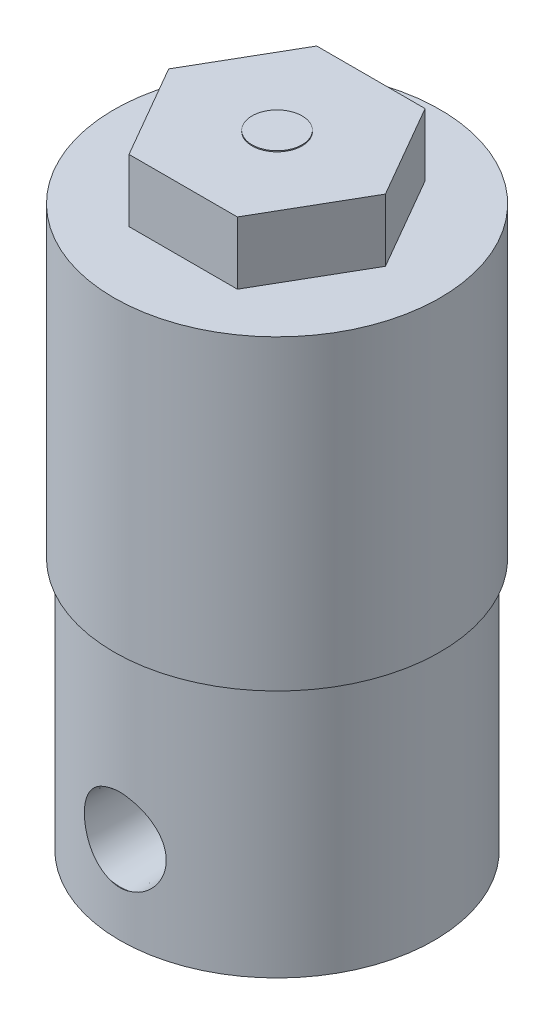
SolidWorks part; units mm, degrees
ref_plane "Plan de face" through (0, 0, 0) normal (0, 0, 1) x (1, 0, 0)
ref_plane "Plan de dessus" through (0, 0, 0) normal (0, 1, 0) x (1, 0, 0)
ref_plane "Plan de droite" through (0, 0, 0) normal (1, 0, 0) x (0, 0, -1)
sketch "Esquisse1" plane through (0, 0, 0) normal (0, 1, 0) x (1, 0, 0)
  circle A0 centre (0, 0) radius 12.56
extrude "Boss.-Extru.1" add sketch "Esquisse1" along normal blind 20.19 contours A0
ref_plane "Plan1" through (0, 0, 12.56) normal (0, 0, 1) x (1, 0, 0)
hole_wizard "Trou taraudé 1/8 Rc1" positions "Esquisse8" profile "Esquisse9" size "1/8" standard "KS"
sketch "Esquisse8" plane through (0, 0, 12.56) normal (0, 0, 1) x (1, 0, 0)
  line L0 (0, -14.333) -> (0, 14.333) construction
  line L1 (14.333, 0) -> (-14.333, 0) construction
  point P0 (0, 6.96)
  dimension "D1" = 6.96
sketch "Esquisse9" plane through (0, 6.96, 12.56) normal (1, 0, 0) x (0, -1, 0)
  line L0 (0, 0) -> (0, 10.8734)
  line L1 (3.95, 8.5) -> (0, 10.8734)
  line L2 (-3.95, 8.5) -> (0, 10.8734) construction
  line L3 (3.95, 8.5) -> (3.95, 7.4)
  line L4 (3.95, 7.4) -> (3.0528, 7.4)
  line L5 (3.0528, 7.4) -> (3.283, 0.025)
  line L6 (3.283, 0.025) -> (3.308, 0)
  line L7 (3.308, 0) -> (0, 0)
  line L8 (0, -6.35) -> (0, 107.95) construction
  line L9 (-3.283, 0.025) -> (-3.308, 0) construction
  line L11 (-3.95, 7.4) -> (-3.0528, 7.4) construction
  line L12 (-3.0528, 7.4) -> (-3.283, 0.025) construction
  dimension "Diamètre du trou pour taraudage" = 7.9
  dimension "Profondeur du trou pour taraudage" = 8.5
  dimension "Diamètre du filetage" = 6.566
  dimension "Angle de filetage" = 3.576
  dimension "Profondeur du filetage" = 7.4
  dimension "Diamètre du fraisage" = 6.616
  dimension "Angle du fraisage" = 90
  dimension "Angle de pointe" = 118
hole_wizard "Trou taraudé 1/8 Rc2" positions "Esquisse3D1" profile "Esquisse12" size "1/8" standard "KS"
sketch3d "Esquisse3D1"
  point P0 (0, 6.9496, -12.56)
sketch "Esquisse12" plane through (0, 6.9496, -12.56) normal (1, 0, 0) x (0, 1, 0)
  line L0 (0, 0) -> (0, 10.8734)
  line L1 (3.95, 8.5) -> (0, 10.8734)
  line L2 (-3.95, 8.5) -> (0, 10.8734) construction
  line L3 (3.95, 8.5) -> (3.95, 7.4)
  line L4 (3.95, 7.4) -> (3.0528, 7.4)
  line L5 (3.0528, 7.4) -> (3.283, 0.025)
  line L6 (3.283, 0.025) -> (3.308, 0)
  line L7 (3.308, 0) -> (0, 0)
  line L8 (0, -6.35) -> (0, 107.95) construction
  line L9 (-3.283, 0.025) -> (-3.308, 0) construction
  line L11 (-3.95, 7.4) -> (-3.0528, 7.4) construction
  line L12 (-3.0528, 7.4) -> (-3.283, 0.025) construction
  dimension "Diamètre du trou pour taraudage" = 7.9
  dimension "Profondeur du trou pour taraudage" = 8.5
  dimension "Diamètre du filetage" = 6.566
  dimension "Angle de filetage" = 3.576
  dimension "Profondeur du filetage" = 7.4
  dimension "Diamètre du fraisage" = 6.616
  dimension "Angle du fraisage" = 90
  dimension "Angle de pointe" = 118
sketch "Esquisse13" plane through (0, 20.19, 0) normal (0, 1, 0) x (1, 0, 0)
  circle A0 centre (0, 0) radius 2
  dimension "D1" = 4
extrude "Boss.-Extru.2" add sketch "Esquisse13" along normal blind 29.59
sketch "Esquisse14" plane through (0, 20.19, 0) normal (0, 1, 0) x (1, 0, 0)
  circle A0 centre (0, 0) radius 13.03
  dimension "D1" = 26.06
extrude "Boss.-Extru.3" add sketch "Esquisse14" along normal blind 24.51
sketch "Esquisse16" plane through (0, 44.7, 0) normal (0, 1, 0) x (1, 0, 0)
  line L1 (8.6603, 0) -> (4.3301, 7.5)
  line L2 (4.3301, 7.5) -> (-4.3301, 7.5)
  line L3 (-4.3301, 7.5) -> (-8.6603, 0)
  line L4 (-8.6603, 0) -> (-4.3301, -7.5)
  line L5 (-4.3301, -7.5) -> (4.3301, -7.5)
  line L6 (4.3301, -7.5) -> (8.6603, 0)
  circle A0 centre (0, 0) radius 7.5 construction
  dimension "D1" = 15
extrude "Boss.-Extru.4" add sketch "Esquisse16" along normal blind 5
sketch "Esquisse17" plane through (0, 0, 0) normal (0, -1, 0) x (1, 0, 0)
  line L0 (14.333, 0) -> (-14.333, 0) construction
  circle A0 centre (-9.335, 0) radius 0.5
  circle A1 centre (9.335, 0) radius 0.5
  dimension "D3" = 1
  dimension "D4" = 1
  dimension "D1" = 9.335
  dimension "D2" = 9.335
hole_wizard "Dégagement #81" positions "Esquisse3D2" profile "Esquisse18" hole size "#8" standard "Ansi Inch"
sketch3d "Esquisse3D2"
  point P0 (-9.335, 0, 0)
  point P3 (9.335, 0, 0)
sketch "Esquisse18" plane through (-9.335, 0, 0) normal (1, 0, 0) x (0, 0, -1)
  line L0 (0, 0) -> (0, 10)
  line L1 (0, 10) -> (2.2479, 8.6493)
  line L2 (2.2479, 8.6493) -> (2.2479, 0.635)
  line L3 (2.2479, 0.635) -> (2.8829, 0)
  line L5 (2.8829, 0) -> (0, 0)
  line L6 (-2.2479, 0.635) -> (-2.8829, 0) construction
  line L10 (0, 10) -> (-2.2479, 8.6493) construction
  line L11 (0, -6.35) -> (0, 107.95) construction
  dimension "Diamètre du perçage" = 4.4958
  dimension "Profondeur du perçage" = 10
  dimension "Diamètre du fraisage entrant" = 5.7658
  dimension "Angle du fraisage entrant" = 90
  dimension "Angle de pointe" = 118
